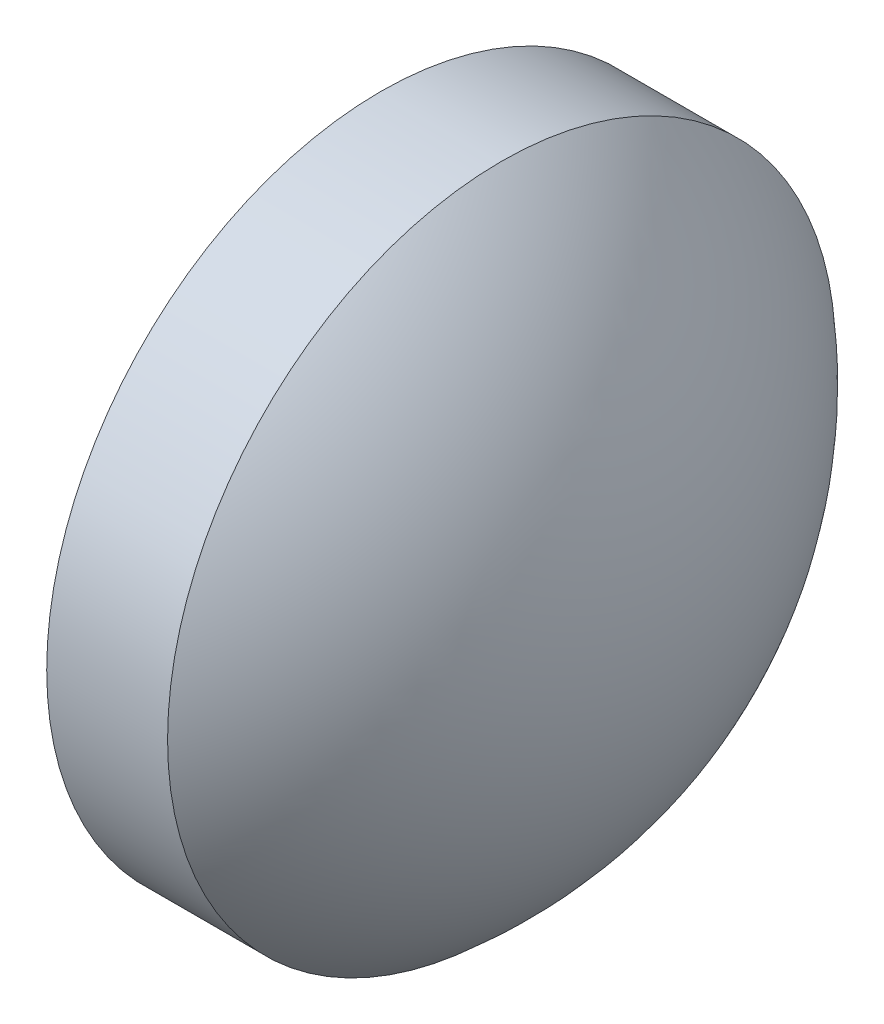
SolidWorks part; units mm, degrees
ref_plane "前视基准面" through (0, 0, 0) normal (0, 0, 1) x (1, 0, 0)
ref_plane "上视基准面" through (0, 0, 0) normal (0, 1, 0) x (1, 0, 0)
ref_plane "右视基准面" through (0, 0, 0) normal (1, 0, 0) x (0, 0, -1)
sketch "草图1" plane through (0, 0, 0) normal (0, 0, 1) x (1, 0, 0)
  line L0 (429.4681, 112.9187) -> (435.6035, 112.9187) construction
  line L1 (430.3297, 112.9187) -> (430.3297, 116.0687)
  line L2 (430.3297, 116.0687) -> (431.4697, 116.0687)
  line L3 (432.9297, 112.9187) -> (430.3297, 112.9187)
  arc A0 (432.9297, 112.9187) -> (431.4697, 116.0687) centre (428.8016, 112.9187) ccw
revolve "旋转1" add sketch "草图1" angle 360 about L0
